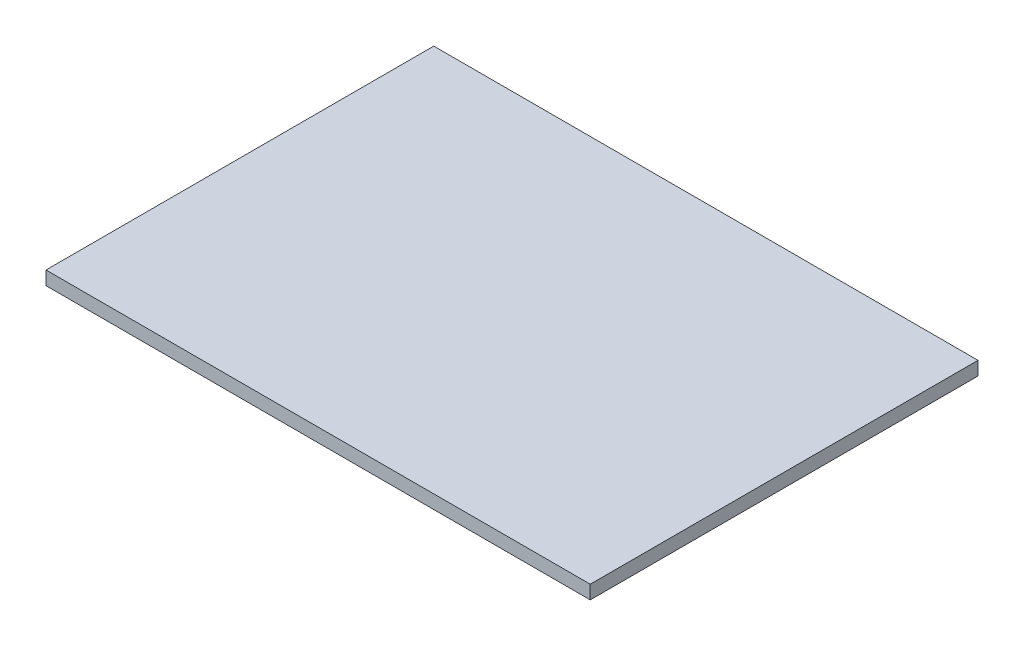
SolidWorks part; units mm, degrees
material "Pino"
ref_plane "Alzado" through (0, 0, 0) normal (0, 0, 1) x (1, 0, 0)
ref_plane "Planta" through (0, 0, 0) normal (0, 1, 0) x (1, 0, 0)
ref_plane "Vista lateral" through (0, 0, 0) normal (1, 0, 0) x (0, 0, -1)
sketch "Sketch1" plane through (0, 0, 0) normal (0, 1, 0) x (1, 0, 0)
  line L1 (-400, -285) -> (400, -285)
  line L2 (-400, -285) -> (-400, 285)
  line L3 (-400, 285) -> (400, 285)
  line L4 (400, -285) -> (400, 285)
  line L5 (-400, -285) -> (400, 285) construction
  line L6 (-400, 285) -> (400, -285) construction
  point P0 (0, 0)
  dimension "D1" = 800
  dimension "D2" = 570
extrude "Extrude1" add sketch "Sketch1" along normal blind 20
